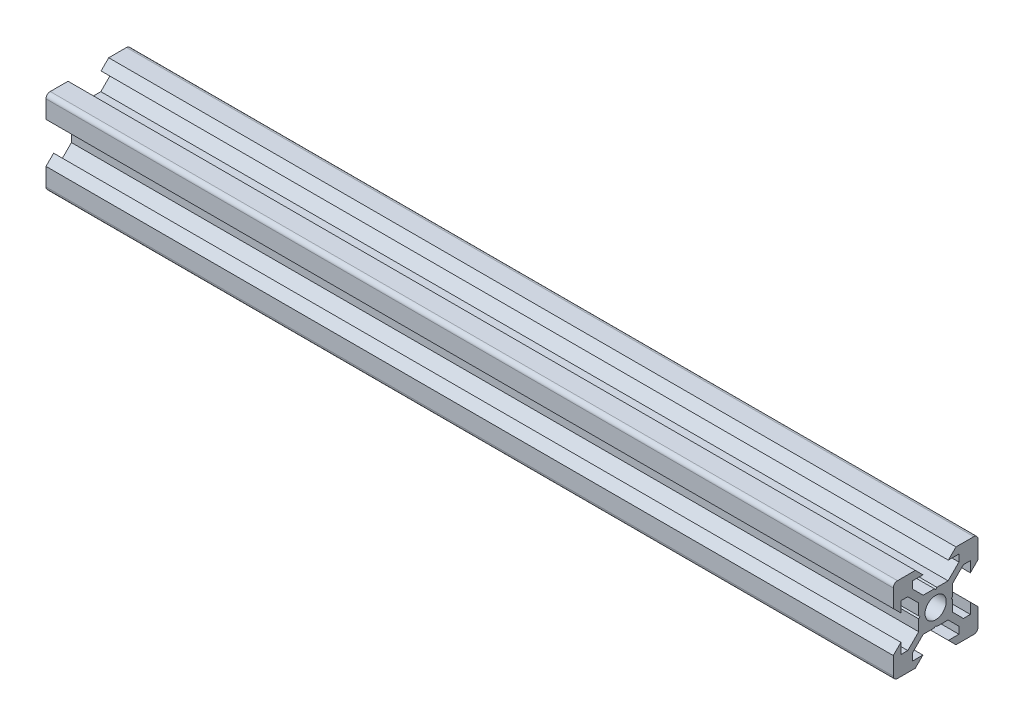
SolidWorks part; units mm, degrees
material "6063-T5"
material "6063-T5"
ref_plane "Plano frontal" through (0, 0, 0) normal (0, 0, 1) x (1, 0, 0)
ref_plane "Plano superior" through (0, 0, 0) normal (0, 1, 0) x (1, 0, 0)
ref_plane "Plano direito" through (0, 0, 0) normal (1, 0, 0) x (0, 0, -1)
sketch "Esboço1" plane through (0, 0, 0) normal (0, 0, 1) x (1, 0, 0)
  line L0 (0, 0) -> (200, 0)
  dimension "D1" = 200
other "Quadrado PF20-11 - PERFIL 2020 V-SLOT(1)"
ref_plane "Plano1" through (0, 0, 0) normal (1, 0, 0) x (0, 1, 0)
sketch "Sketch11" plane through (0, 0, 0) normal (1, 0, 0) x (0, 1, 0)
  line L0 (-4.8, 10) -> (-3, 8.2)
  line L1 (-3, 8.2) -> (-5.5, 8.2)
  line L2 (-5.5, 8.2) -> (-5.5, 6.5607)
  line L3 (-5.5, 6.5607) -> (-2.9393, 4)
  line L4 (-2.9393, 4) -> (-0.3, 4)
  line L5 (5.5, 6.5607) -> (2.9393, 4)
  line L6 (5.5, 8.2) -> (5.5, 6.5607)
  line L7 (3, 8.2) -> (5.5, 8.2)
  line L8 (4.8, 10) -> (3, 8.2)
  line L9 (-0.3, 4) -> (0, 3.7)
  line L10 (0.3, 4) -> (0, 3.7)
  line L11 (0.3, 4) -> (2.9393, 4)
  line L12 (9, 10) -> (4.8, 10)
  line L13 (10, 4.8) -> (8.2, 3)
  line L14 (10, 4.8) -> (10, 9)
  line L15 (8.2, 3) -> (8.2, 5.5)
  line L16 (8.2, 5.5) -> (6.5607, 5.5)
  line L17 (6.5607, 5.5) -> (4, 2.9393)
  line L18 (4.8, -10) -> (3, -8.2)
  line L19 (3, -8.2) -> (5.5, -8.2)
  line L20 (5.5, -8.2) -> (5.5, -6.5607)
  line L21 (5.5, -6.5607) -> (2.9393, -4)
  line L22 (2.9393, -4) -> (0.3, -4)
  line L23 (0.3, -4) -> (0, -3.7)
  line L24 (-0.3, -4) -> (0, -3.7)
  line L25 (-0.3, -4) -> (-2.9393, -4)
  line L26 (-5.5, -6.5607) -> (-2.9393, -4)
  line L27 (-5.5, -8.2) -> (-5.5, -6.5607)
  line L28 (-3, -8.2) -> (-5.5, -8.2)
  line L29 (-4.8, -10) -> (-3, -8.2)
  line L30 (-10, -4.8) -> (-10, -9)
  line L31 (-10, -4.8) -> (-8.2, -3)
  line L32 (-8.2, -3) -> (-8.2, -5.5)
  line L33 (-8.2, -5.5) -> (-6.5607, -5.5)
  line L34 (-6.5607, -5.5) -> (-4, -2.9393)
  line L35 (-4, -2.9393) -> (-4, -0.3)
  line L36 (-4, -0.3) -> (-3.7, 0)
  line L37 (-4, 0.3) -> (-3.7, 0)
  line L38 (-4, 0.3) -> (-4, 2.9393)
  line L39 (-6.5607, 5.5) -> (-4, 2.9393)
  line L40 (-8.2, 5.5) -> (-6.5607, 5.5)
  line L41 (-8.2, 3) -> (-8.2, 5.5)
  line L42 (-10, 4.8) -> (-8.2, 3)
  line L43 (-4.8, 10) -> (-9, 10)
  line L44 (4, 2.9393) -> (4, 0.3)
  line L45 (4, 0.3) -> (3.7, 0)
  line L46 (4, -0.3) -> (3.7, 0)
  line L47 (4, -0.3) -> (4, -2.9393)
  line L48 (6.5607, -5.5) -> (4, -2.9393)
  line L49 (8.2, -5.5) -> (6.5607, -5.5)
  line L50 (8.2, -3) -> (8.2, -5.5)
  line L51 (10, -4.8) -> (8.2, -3)
  line L52 (10, -9) -> (10, -4.8)
  line L53 (4.8, -10) -> (9, -10)
  line L106 (-10, 9) -> (-10, 4.8)
  line L107 (-9, -10) -> (-4.8, -10)
  arc A0 (10, 9) -> (9, 10) centre (9, 9) ccw
  arc A1 (9, -10) -> (10, -9) centre (9, -9) ccw
  arc A3 (-10, -9) -> (-9, -10) centre (-9, -9) ccw
  arc A4 (-9, 10) -> (-10, 9) centre (-9, 9) ccw
  circle A7 centre (0, 0) radius 2.5
  point P1 (-10, 10)
  point P3 (10, 10)
  point P4 (10, -10)
  point P68 (0, 0)
  point P70 (10, 0)
  point P71 (0, 0)
  point P72 (0, 0)
  point P113 (0, -10)
  point P114 (-10, -10)
  point P115 (-10, 0)
  point P116 (0, 10)
  point P118 (0, 0)
